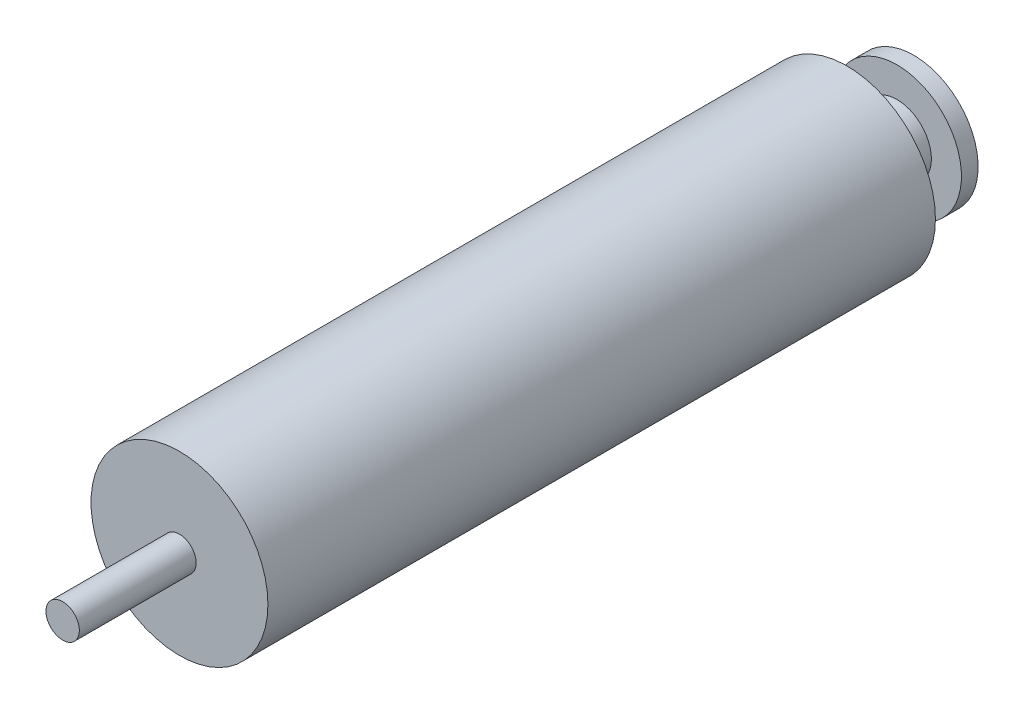
SolidWorks part; units mm, degrees
ref_plane "Front Plane" through (0, 0, 0) normal (0, 0, 1) x (1, 0, 0)
ref_plane "Top Plane" through (0, 0, 0) normal (0, 1, 0) x (1, 0, 0)
ref_plane "Right Plane" through (0, 0, 0) normal (1, 0, 0) x (0, 0, -1)
sketch "Sketch2" plane through (0, 0, 0) normal (0, 0, 1) x (1, 0, 0)
  line L0 (0, 0) -> (29.6985, 29.6985) construction
  line L1 (0, 0) -> (42, 0) construction
  circle A0 centre (0, 0) radius 75 construction
  circle A1 centre (29.6985, 29.6985) radius 26.5
  circle A2 centre (0, 0) radius 42 construction
  point P6 (0, 0)
  dimension "D2" = 150
extrude "Boss-Extrude1" add sketch "Sketch2" along normal blind 200
sketch "Sketch3" plane through (0, 0, 200) normal (0, 0, 1) x (1, 0, 0)
  circle A0 centre (29.6985, 29.6985) radius 5
extrude "Boss-Extrude2" add sketch "Sketch3" along normal blind 35
sketch "Sketch4" plane through (0, 0, 0) normal (0, 0, -1) x (-1, 0, 0)
  circle A0 centre (-29.6985, 29.6985) radius 10.2714
extrude "Boss-Extrude3" add sketch "Sketch4" along normal blind 15
sketch "Sketch5" plane through (0, 0, -15) normal (0, 0, -1) x (-1, 0, 0)
  circle A0 centre (-29.6985, 29.6985) radius 19.2883
extrude "Boss-Extrude4" add sketch "Sketch5" along normal blind 5
